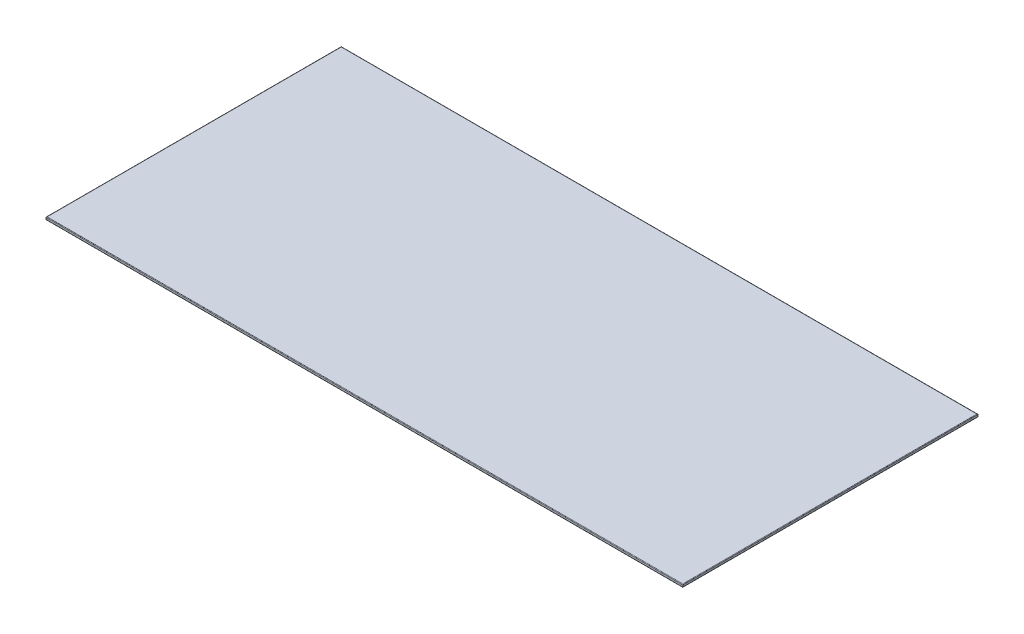
SolidWorks part; units mm, degrees
ref_plane "Ebene vorne" through (0, 0, 0) normal (0, 0, 1) x (1, 0, 0)
ref_plane "Ebene oben" through (0, 0, 0) normal (0, 1, 0) x (1, 0, 0)
ref_plane "Ebene rechts" through (0, 0, 0) normal (1, 0, 0) x (0, 0, -1)
sketch "Sketch1" plane through (0, 0, 0) normal (0, 1, 0) x (1, 0, 0)
  line L1 (-578, -268) -> (578, -268)
  line L2 (-578, -268) -> (-578, 268)
  line L3 (-578, 268) -> (578, 268)
  line L4 (578, -268) -> (578, 268)
  line L5 (-578, -268) -> (578, 268) construction
  line L6 (-578, 268) -> (578, -268) construction
  point P0 (0, 0)
  dimension "D1" = 536
  dimension "D2" = 1156
extrude "Boss-Extrude1" add sketch "Sketch1" along normal blind 5
fillet "Fillet1" radius 1 8 edges at (-578, 0, 0) (0, 0, -268) (0, 0, 268) (578, 0, 0) (578, 5, 0) (0, 5, -268) (-578, 5, 0) (0, 5, 268)
